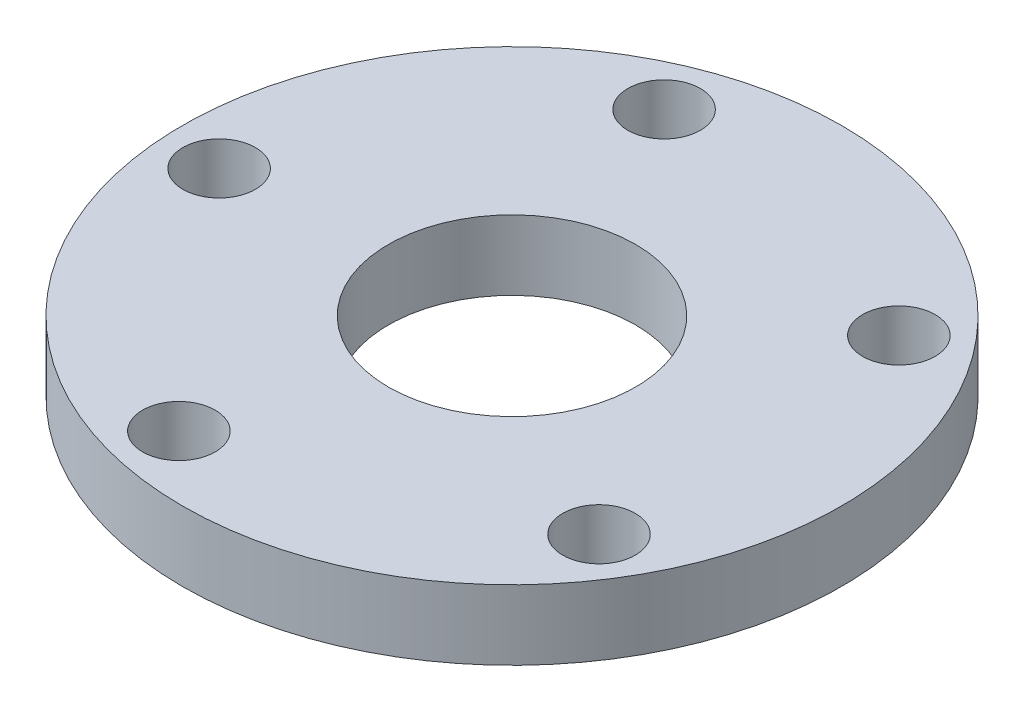
SolidWorks part; units mm, degrees
ref_plane "Front Plane" through (0, 0, 0) normal (0, 0, 1) x (1, 0, 0)
ref_plane "Top Plane" through (0, 0, 0) normal (0, 1, 0) x (1, 0, 0)
ref_plane "Right Plane" through (0, 0, 0) normal (1, 0, 0) x (0, 0, -1)
sketch "Sketch3" plane through (0, 0, 0) normal (0, 0, 1) x (1, 0, 0)
  line L1 (0, 0) -> (60, 0)
  line L2 (0, 0) -> (0, 6.35)
  line L3 (0, 6.35) -> (60, 6.35)
  line L4 (60, 0) -> (60, 6.35)
  dimension "D1" = 60
  dimension "D2" = 6.35
extrude "Boss-Extrude2" add sketch "Sketch3" along normal blind 60
sketch "Sketch4" plane through (0, 6.35, 0) normal (0, 1, 0) x (1, 0, 0)
  line L0 (0, -60) -> (0, 0) construction
  line L1 (60, -60) -> (0, -60) construction
  circle A0 centre (30, -30) radius 11.25
  point P4 (0, -30)
  point P7 (30, -60)
  dimension "D1" = 22.5
extrude "Cut-Extrude2" cut sketch "Sketch4" against normal through all
sketch "Sketch5" plane through (0, 6.35, 0) normal (0, 1, 0) x (1, 0, 0)
  circle A3 centre (20.6584, -6.8109) radius 3.302
  circle A4 centre (49.1674, -13.9498) radius 3.302
  circle A5 centre (51.1877, -43.2695) radius 3.302
  circle A6 centre (23.9273, -54.2512) radius 3.302
  circle A7 centre (5.0591, -31.7185) radius 3.302
  point P0 (30, -30)
  point P14 (30, -30)
  dimension "D1" = 25
  dimension "D2" = 6.604
  dimension "D3" = 5
extrude "Cut-Extrude3" cut sketch "Sketch5" against normal through all
sketch "Sketch6" plane through (0, 6.35, 0) normal (0, 1, 0) x (1, 0, 0)
  line L4 (60, 0) -> (0, 0)
  line L5 (0, 0) -> (0, -60)
  line L6 (0, -60) -> (60, -60)
  line L7 (60, -60) -> (60, 0)
  line L8 (60, 0) -> (0, 0)
  line L9 (0, 0) -> (0, -60)
  line L10 (0, -60) -> (60, -60)
  line L11 (60, -60) -> (60, 0)
  circle A0 centre (30, -30) radius 30
  line M7 (60, 0) -> (0, 0)
  line M8 (0, 0) -> (0, -60)
  line M9 (0, -60) -> (60, -60)
  line M10 (60, -60) -> (60, 0)
  dimension "D1" = 0
extrude "Cut-Extrude4" cut sketch "Sketch6" against normal through all contours A0 L8 M8 | A0 L11 M7 | A0 L10 M10 | A0 L9 M9
